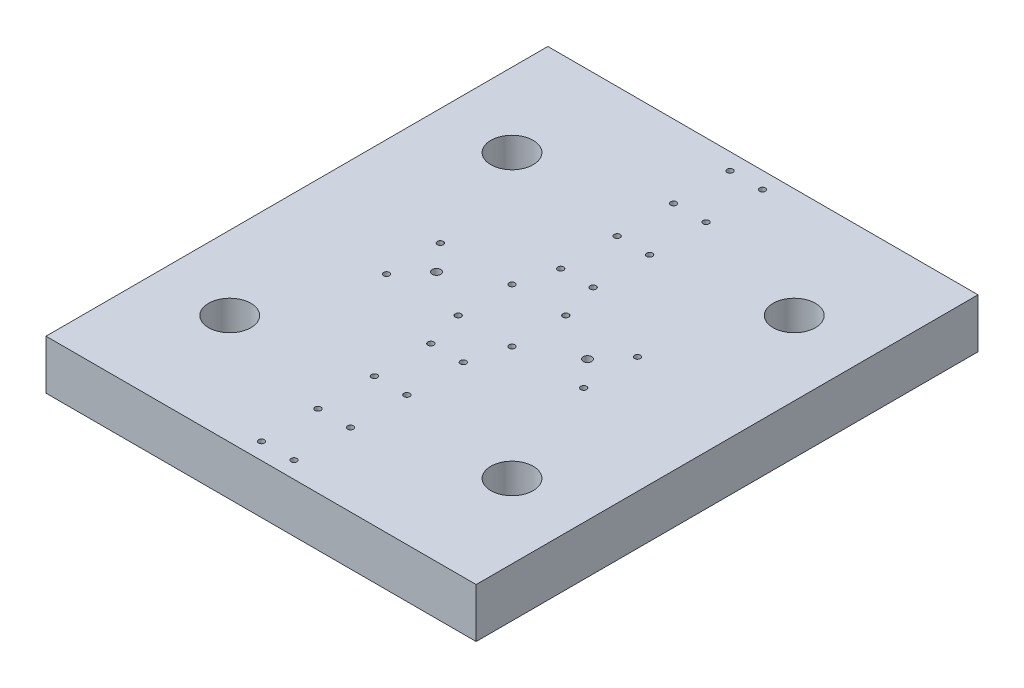
SolidWorks part; units mm, degrees
material "201 Annealed Stainless Steel (SS)"
ref_plane "Front Plane" through (0, 0, 0) normal (0, 0, 1) x (1, 0, 0)
ref_plane "Top Plane" through (0, 0, 0) normal (0, 1, 0) x (1, 0, 0)
ref_plane "Right Plane" through (0, 0, 0) normal (1, 0, 0) x (0, 0, -1)
sketch "Sketch2" plane through (0, 0, 0) normal (0, 1, 0) x (1, 0, 0)
  line L1 (152.4, -177.8) -> (-152.4, -177.8)
  line L2 (152.4, -177.8) -> (152.4, 177.8)
  line L3 (152.4, 177.8) -> (-152.4, 177.8)
  line L4 (-152.4, -177.8) -> (-152.4, 177.8)
  line L5 (152.4, -177.8) -> (-152.4, 177.8) construction
  line L6 (152.4, 177.8) -> (-152.4, -177.8) construction
  point P0 (0, 0)
  dimension "D1" = 355.6
  dimension "D2" = 304.8
extrude "MainBase_Extrude" add sketch "Sketch2" along normal mid plane 35
sketch "Sketch3" plane through (0, 17.5, 0) normal (0, 1, 0) x (1, 0, 0)
  line L2 (100, -100) -> (-100, -100) construction
  line L3 (100, -100) -> (100, 100) construction
  line L4 (100, 100) -> (-100, 100) construction
  line L5 (-100, -100) -> (-100, 100) construction
  line L6 (100, -100) -> (-100, 100) construction
  line L7 (100, 100) -> (-100, -100) construction
  circle A0 centre (-100, 100) radius 15
  circle A1 centre (100, 100) radius 15
  circle A2 centre (100, -100) radius 15
  circle A3 centre (-100, -100) radius 15
  point P2 (0, 0)
  dimension "D3" = 30
  dimension "D1" = 200
  dimension "D2" = 200
extrude "Holes_Pole" cut sketch "Sketch3" against normal through all
sketch "MotorMountScrewPos" plane through (0, 17.5, 0) normal (0, 1, 0) x (1, 0, 0)
  line L0 (0, -177.8) -> (0, 177.8) construction
  line L1 (152.4, 177.8) -> (-152.4, 177.8) construction
  line L2 (19.05, 19.05) -> (69.85, -19.05) construction
  line L3 (-19.05, -19.05) -> (-69.85, -19.05) construction
  line L4 (-19.05, -19.05) -> (-19.05, 19.05) construction
  line L5 (-19.05, 19.05) -> (-69.85, 19.05) construction
  line L6 (-69.85, -19.05) -> (-69.85, 19.05) construction
  line L7 (-19.05, -19.05) -> (-69.85, 19.05) construction
  line L8 (-19.05, 19.05) -> (-69.85, -19.05) construction
  line L9 (19.05, -19.05) -> (69.85, 19.05) construction
  line L10 (69.85, -19.05) -> (69.85, 19.05) construction
  line L11 (19.05, 19.05) -> (69.85, 19.05) construction
  line L12 (19.05, -19.05) -> (19.05, 19.05) construction
  line L13 (19.05, -19.05) -> (69.85, -19.05) construction
  point P0 (-44.45, 0)
  point P6 (0, 0)
  point P16 (44.45, 0)
  point P17 (-19.05, 19.05)
  point P18 (-69.85, 19.05)
  point P19 (-19.05, -19.05)
  point P20 (-69.85, -19.05)
  point P21 (19.05, -19.05)
  point P22 (19.05, 19.05)
  point P23 (69.85, 19.05)
  point P24 (69.85, -19.05)
  dimension "D1" = 19.05
  dimension "D2" = 50.8
  dimension "D3" = 38.1
hole_wizard "M5x0.8 Tapped Hole1" positions "Sketch5" profile "Sketch6" tap size "M5x0.8" standard "ANSI Metric" end condition through all
sketch "Sketch5" plane through (0, 17.5, 0) normal (0, 1, 0) x (1, 0, 0)
  point P0 (-69.85, 19.05)
  point P3 (-19.05, 19.05)
  point P6 (-19.05, -19.05)
  point P9 (-69.85, -19.05)
  point P12 (19.05, 19.05)
  point P15 (19.05, -19.05)
  point P18 (69.85, -19.05)
  point P21 (69.85, 19.05)
sketch "Sketch6" plane through (-69.85, 17.5, -19.05) normal (1, 0, 0) x (0, 0, 1)
  line L0 (0, 0) -> (0, 35)
  line L1 (0, 35) -> (2.1, 35)
  line L2 (2.1, 35) -> (2.1, 0)
  line L5 (2.1, 0) -> (0, 0)
  line L11 (0, -6.35) -> (0, 107.95) construction
  dimension "Thru Tap Drill Dia." = 4.2
  dimension "Thru Tap Drill Depth" = 35
cosmetic thread "Hole Thread1" parameters "D2"=5
cosmetic thread "Hole Thread2" parameters "D2"=5
cosmetic thread "Hole Thread3" parameters "D2"=5
cosmetic thread "Hole Thread4" parameters "D2"=5
cosmetic thread "Hole Thread5" parameters "D2"=5
cosmetic thread "Hole Thread6" parameters "D2"=5
cosmetic thread "Hole Thread7" parameters "D2"=5
cosmetic thread "Hole Thread8" parameters "D2"=5
sketch "LinearRailHolePos" plane through (0, 17.5, 0) normal (0, 1, 0) x (1, 0, 0)
  point P0 (-11.5, -45.9918)
  point P1 (11.5, -45.9918)
  point P3 (11.5, -85.9918)
  point P5 (-11.5, -85.9918)
  point P7 (-11.5, -125.9918)
  point P9 (11.5, -125.9918)
  point P11 (11.5, -165.9918)
  point P13 (-11.5, -165.9918)
hole_wizard "M5x0.8 Tapped Hole2" positions "Sketch8" profile "Sketch9" tap size "M5x0.8" standard "ANSI Metric" end condition through all
sketch "Sketch8" plane through (0, 17.5, 0) normal (0, 1, 0) x (1, 0, 0)
  point P0 (-11.5, -45.9918)
  point P3 (11.5, -45.9918)
  point P6 (11.5, -85.9918)
  point P9 (-11.5, -85.9918)
  point P12 (-11.5, -125.9918)
  point P15 (11.5, -125.9918)
  point P18 (-11.5, -165.9918)
  point P21 (11.5, -165.9918)
sketch "Sketch9" plane through (-11.5, 17.5, 45.9918) normal (1, 0, 0) x (0, 0, 1)
  line L0 (0, 0) -> (0, 35)
  line L1 (0, 35) -> (2.1, 35)
  line L2 (2.1, 35) -> (2.1, 0)
  line L5 (2.1, 0) -> (0, 0)
  line L11 (0, -6.35) -> (0, 107.95) construction
  dimension "Thru Tap Drill Dia." = 4.2
  dimension "Thru Tap Drill Depth" = 35
cosmetic thread "Hole Thread9" parameters "D2"=5
cosmetic thread "Hole Thread10" parameters "D2"=5
cosmetic thread "Hole Thread11" parameters "D2"=5
cosmetic thread "Hole Thread12" parameters "D2"=5
cosmetic thread "Hole Thread13" parameters "D2"=5
cosmetic thread "Hole Thread14" parameters "D2"=5
cosmetic thread "Hole Thread15" parameters "D2"=5
cosmetic thread "Hole Thread16" parameters "D2"=5
mirror "Mirror1" about plane through (0, 0, 0) normal (0, 0, 1) of "M5x0.8 Tapped Hole2"
cosmetic thread "Hole Thread17" parameters "D2"=5
cosmetic thread "Hole Thread18" parameters "D2"=5
cosmetic thread "Hole Thread19" parameters "D2"=5
cosmetic thread "Hole Thread20" parameters "D2"=5
cosmetic thread "Hole Thread21" parameters "D2"=5
cosmetic thread "Hole Thread22" parameters "D2"=5
cosmetic thread "Hole Thread23" parameters "D2"=5
cosmetic thread "Hole Thread24" parameters "D2"=5
sketch "Sketch10" plane through (0, -17.5, 0) normal (0, -1, 0) x (1, 0, 0)
  point P0 (-64.5, -87.5)
  point P1 (-49.5, -87.5)
  point P3 (-49.5, -142.5)
  point P5 (-64.5, -142.5)
  point P7 (-64.5, -27.5)
  point P9 (-49.5, -27.5)
hole_wizard "M5x0.8 Tapped Hole3" positions "Sketch11" profile "Sketch12" tap size "M5x0.8" standard "ANSI Metric"
sketch "Sketch11" plane through (0, -17.5, 0) normal (0, -1, 0) x (-1, 0, 0)
  point P0 (64.5, 142.5)
  point P3 (49.5, 142.5)
  point P6 (49.5, 87.5)
  point P9 (64.5, 87.5)
  point P13 (49.5, 27.5)
  point P16 (64.5, 27.5)
sketch "Sketch12" plane through (-64.5, -17.5, -142.5) normal (1, 0, 0) x (0, 0, -1)
  line L0 (0, 0) -> (0, 13.6618)
  line L1 (0, 13.6618) -> (2.1, 12.4)
  line L2 (2.1, 12.4) -> (2.1, 0)
  line L5 (2.1, 0) -> (0, 0)
  line L10 (0, 13.6618) -> (-2.1, 12.4) construction
  line L11 (0, -6.35) -> (0, 107.95) construction
  dimension "Tap Drill Dia." = 4.2
  dimension "Tap Drill Depth" = 12.4
  dimension "Drill Angle" = 118
cosmetic thread "Hole Thread25" parameters "D1"=10, "D2"=5
cosmetic thread "Hole Thread26" parameters "D1"=10, "D2"=5
cosmetic thread "Hole Thread27" parameters "D1"=10, "D2"=5
cosmetic thread "Hole Thread28" parameters "D1"=10, "D2"=5
cosmetic thread "Hole Thread29" parameters "D1"=10, "D2"=5
cosmetic thread "Hole Thread30" parameters "D1"=10, "D2"=5
mirror "Mirror2" about plane through (0, 0, 0) normal (0, 0, 1) of "M5x0.8 Tapped Hole3"
cosmetic thread "Hole Thread31" parameters "D1"=10, "D2"=5
cosmetic thread "Hole Thread32" parameters "D1"=10, "D2"=5
cosmetic thread "Hole Thread33" parameters "D1"=10, "D2"=5
cosmetic thread "Hole Thread34" parameters "D1"=10, "D2"=5
cosmetic thread "Hole Thread35" parameters "D1"=10, "D2"=5
cosmetic thread "Hole Thread36" parameters "D1"=10, "D2"=5
mirror "Mirror3" about plane through (0, 0, 0) normal (1, 0, 0) of "Mirror2", "M5x0.8 Tapped Hole3"
cosmetic thread "Hole Thread37" parameters "D1"=10, "D2"=5
cosmetic thread "Hole Thread38" parameters "D1"=10, "D2"=5
cosmetic thread "Hole Thread39" parameters "D1"=10, "D2"=5
cosmetic thread "Hole Thread40" parameters "D1"=10, "D2"=5
cosmetic thread "Hole Thread41" parameters "D1"=10, "D2"=5
cosmetic thread "Hole Thread42" parameters "D1"=10, "D2"=5
cosmetic thread "Hole Thread43" parameters "D1"=10, "D2"=5
cosmetic thread "Hole Thread44" parameters "D1"=10, "D2"=5
cosmetic thread "Hole Thread45" parameters "D1"=10, "D2"=5
cosmetic thread "Hole Thread46" parameters "D1"=10, "D2"=5
cosmetic thread "Hole Thread47" parameters "D1"=10, "D2"=5
cosmetic thread "Hole Thread48" parameters "D1"=10, "D2"=5
sketch "Sketch13" plane through (0, 17.5, 0) normal (0, 1, 0) x (1, 0, 0)
  point P0 (53.5, 0)
sketch "Sketch14" plane through (0, 17.5, 0) normal (0, 1, 0) x (1, 0, 0)
  circle A0 centre (53.5, 0) radius 3
  dimension "D1" = 6
extrude "Cut-Extrude1" cut sketch "Sketch14" against normal blind 10
mirror "Mirror4" about plane through (0, 0, 0) normal (1, 0, 0) of "Cut-Extrude1"
